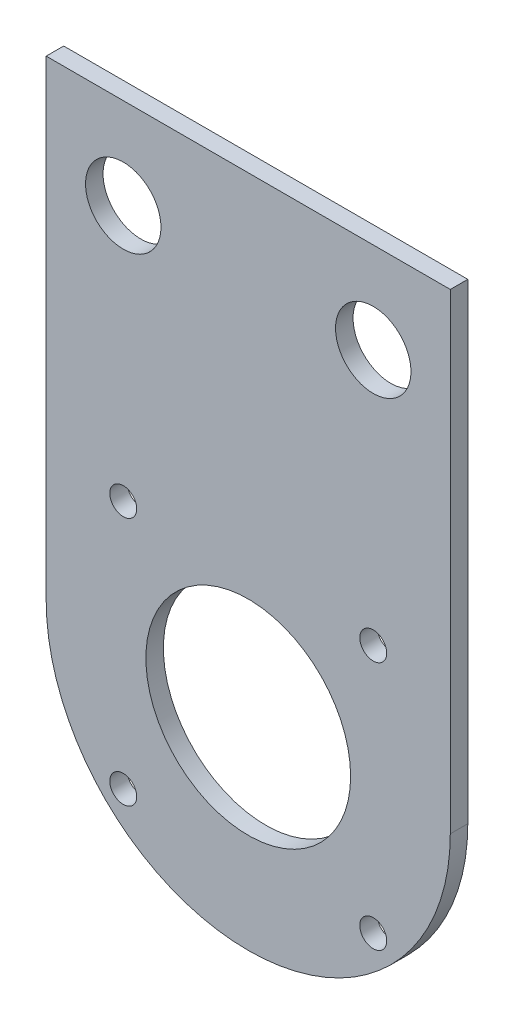
SolidWorks part; units mm, degrees
ref_plane "Front Plane" through (0, 0, 0) normal (0, 0, 1) x (1, 0, 0)
ref_plane "Top Plane" through (0, 0, 0) normal (0, 1, 0) x (1, 0, 0)
ref_plane "Right Plane" through (0, 0, 0) normal (1, 0, 0) x (0, 0, -1)
sketch "Sketch1" plane through (0, 0, 0) normal (0, 0, 1) x (1, 0, 0)
  line L0 (0, 88.9) -> (0, -38.1) construction
  line L1 (-38.1, 0) -> (38.1, 0) construction
  line L2 (-38.1, 0) -> (-38.1, 88.9)
  line L3 (-38.1, 88.9) -> (38.1, 88.9)
  line L4 (38.1, 0) -> (38.1, 88.9)
  circle A0 centre (23.57, 71.755) radius 7.112
  circle A1 centre (23.57, 23.495) radius 2.54
  circle A2 centre (-23.57, -23.495) radius 2.54
  circle A3 centre (-23.57, 23.495) radius 2.54
  circle A4 centre (-23.57, 71.755) radius 7.112
  circle A5 centre (23.57, -23.495) radius 2.54
  circle A6 centre (0, 0) radius 19.304
  arc A7 (-38.1, 0) -> (38.1, 0) centre (0, 0) ccw
  point P13 (0, 0)
  dimension "D2" = 46.99
  dimension "D4" = 76.2
  dimension "D5" = 5.08
  dimension "D7" = 14.224
  dimension "D8" = 38.608
  dimension "D1" = 88.9
  dimension "D3" = 47.14
  dimension "D6" = 95.25
extrude "Boss-Extrude1" add sketch "Sketch1" along normal blind 3.302
